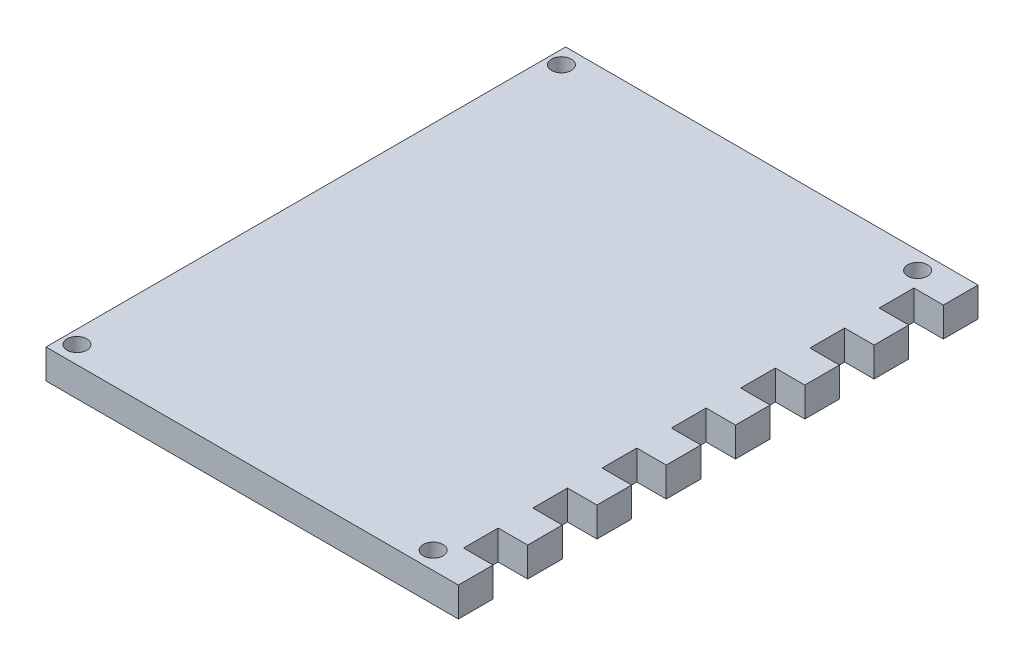
SolidWorks part; units mm, degrees
ref_plane "Front Plane" through (0, 0, 0) normal (0, 0, 1) x (1, 0, 0)
ref_plane "Top Plane" through (0, 0, 0) normal (0, 1, 0) x (1, 0, 0)
ref_plane "Right Plane" through (0, 0, 0) normal (1, 0, 0) x (0, 0, -1)
sketch "Sketch1" plane through (0, 0, 0) normal (0, 1, 0) x (1, 0, 0)
  line L0 (0, 42) -> (61.9, 42) construction
  line L1 (0, 0) -> (61.9, 0)
  line L2 (0, 0) -> (0, 84)
  line L3 (0, 84) -> (61.9, 84)
  line L5 (30.95, 84) -> (30.95, 0) construction
  line L6 (61.9, 84) -> (66.6625, 84)
  line L7 (66.6625, 84) -> (66.6625, 78.4)
  line L8 (66.6625, 78.4) -> (61.9, 78.4)
  line L9 (61.9, 78.4) -> (61.9, 72.8)
  line L10 (61.9, 72.8) -> (66.6625, 72.8)
  line L11 (66.6625, 72.8) -> (66.6625, 67.2)
  line L12 (66.6625, 67.2) -> (61.9, 67.2)
  line L14 (61.9, 5.6) -> (66.6625, 5.6)
  line L15 (66.6625, 5.6) -> (66.6625, 0)
  line L16 (66.6625, 0) -> (61.9, 0)
  line L17 (61.9, 67.2) -> (61.9, 61.6)
  line L18 (61.9, 61.6) -> (66.6625, 61.6)
  line L19 (66.6625, 61.6) -> (66.6625, 56)
  line L20 (66.6625, 56) -> (61.9, 56)
  line L21 (61.9, 56) -> (61.9, 50.4)
  line L22 (61.9, 50.4) -> (66.6625, 50.4)
  line L23 (66.6625, 50.4) -> (66.6625, 44.8)
  line L24 (66.6625, 44.8) -> (61.9, 44.8)
  line L25 (61.9, 44.8) -> (61.9, 39.2)
  line L26 (61.9, 39.2) -> (66.6625, 39.2)
  line L27 (66.6625, 39.2) -> (66.6625, 33.6)
  line L28 (66.6625, 33.6) -> (61.9, 33.6)
  line L29 (61.9, 33.6) -> (61.9, 28)
  line L30 (61.9, 28) -> (66.6625, 28)
  line L31 (66.6625, 28) -> (66.6625, 22.4)
  line L32 (66.6625, 22.4) -> (61.9, 22.4)
  line L33 (61.9, 22.4) -> (61.9, 16.8)
  line L34 (61.9, 16.8) -> (66.6625, 16.8)
  line L35 (66.6625, 16.8) -> (66.6625, 11.2)
  line L36 (66.6625, 11.2) -> (61.9, 11.2)
  line L37 (61.9, 11.2) -> (61.9, 5.6)
  circle A0 centre (2.16, 81.16) radius 1.6
  circle A1 centre (2.16, 2.84) radius 1.6
  circle A2 centre (59.74, 2.84) radius 1.6
  circle A3 centre (59.74, 81.16) radius 1.6
  point P17 (61.9789, 5.6513)
  point P48 (62.2765, 61.2907)
  point P49 (62.2765, 55.8614)
  point P50 (62.0656, 51.3581)
  point P51 (61.9, 48.5662)
  point P52 (0, 0)
  point P53 (0, 0)
  point P54 (61.9, 39.5595)
  point P55 (61.4878, 35.2384)
  point P56 (61.4878, 28.9397)
  point P57 (61.7208, 23.0893)
  point P58 (0, 0)
  point P59 (61.7208, 21.5042)
  point P60 (61.7208, 17.7305)
  point P61 (61.471, 14.5595)
  point P62 (61.2397, 36.0379)
  point P63 (68.25, 69.8227)
  point P64 (61.8582, 61.6)
  point P65 (62.6411, 56)
  point P66 (67.9942, 33.6)
  dimension "D6" = 3.2
  dimension "D1" = 84
  dimension "D2" = 61.9
  dimension "D3" = 4.7625
  dimension "D4" = 2.16
  dimension "D5" = 2.84
extrude "Boss-Extrude1" add sketch "Sketch1" along normal blind 4.7625
